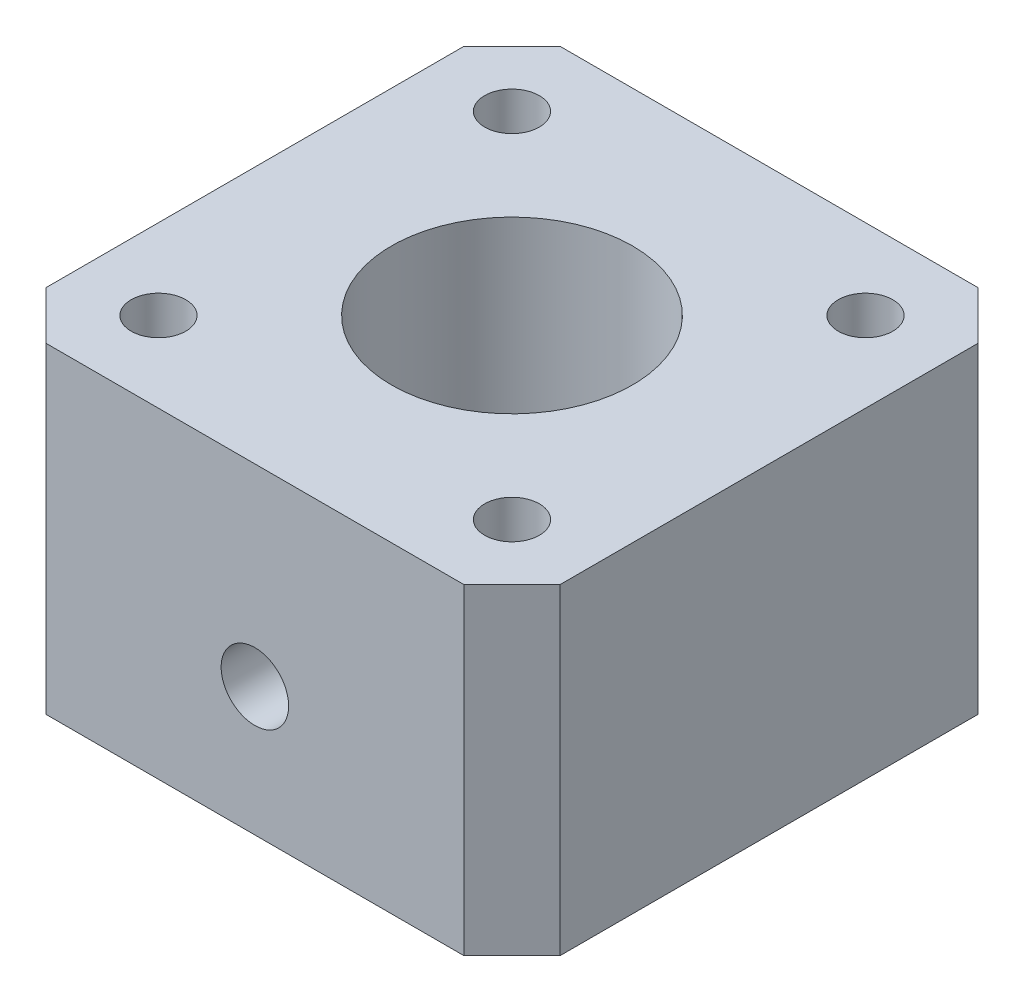
SolidWorks part; units mm, degrees
material "6061-T6 (SS)"
ref_plane "Front Plane" through (0, 0, 0) normal (0, 0, 1) x (1, 0, 0)
ref_plane "Top Plane" through (0, 0, 0) normal (0, 1, 0) x (1, 0, 0)
ref_plane "Right Plane" through (0, 0, 0) normal (1, 0, 0) x (0, 0, -1)
sketch "Sketch1" plane through (0, 0, 0) normal (0, 1, 0) x (1, 0, 0)
  line L0 (-16, 13) -> (-13, 16)
  line L1 (-13, 16) -> (13, 16)
  line L2 (-16, 13) -> (-16, -13)
  line L3 (-13, -16) -> (13, -16)
  line L4 (16, 13) -> (16, -13)
  line L5 (13, 16) -> (16, 13)
  line L6 (13, -16) -> (16, -13)
  line L7 (-16, -13) -> (-13, -16)
  line L8 (-16, 16) -> (-13, 16) construction
  line L9 (-16, 16) -> (-16, 13) construction
  circle A0 centre (0, 0) radius 7.5
  point P3 (-16, 16)
  point P4 (16, -16)
  point P5 (-16, -16)
  point P6 (16, 16)
  point P15 (-16, 0)
  point P16 (0, 16)
  point P17 (0, -16)
  point P18 (16, 0)
  dimension "D1" = 32
  dimension "D3" = 15
  dimension "D2" = 3
extrude "Boss-Extrude1" add sketch "Sketch1" along normal blind 20
sketch "Sketch2" plane through (0, 0, 16) normal (0, 0, 1) x (1, 0, 0)
  point P1 (0, 8)
  dimension "D1" = 8
hole_wizard "M5x0.8 Tapped Hole1" positions "Sketch2" profile "Sketch3" tap size "M5x0.8" standard "ANSI Metric"
cosmetic thread "Hole Thread1" parameters "D1"=10, "D2"=5
sketch "Sketch3" plane through (0, 8, 16) normal (1, 0, 0) x (0, -1, 0)
  line L0 (0, 0) -> (0, 17.2608)
  line L1 (0, 17.2608) -> (2.1, 15.999)
  line L2 (2.1, 15.999) -> (2.1, 0)
  line L5 (2.1, 0) -> (0, 0)
  line L10 (0, 17.2608) -> (-2.1, 15.999) construction
  line L11 (0, -6.35) -> (0, 107.95) construction
  dimension "Tap Drill Dia." = 4.2
  dimension "Tap Drill Depth" = 15.999
  dimension "Drill Angle" = 118
sketch "Sketch4" plane through (0, 0, 0) normal (0, -1, 0) x (-1, 0, 0)
  line L0 (-11, 11) -> (-11, -11) construction
  line L1 (-11, -11) -> (11, -11) construction
  line L2 (11, -11) -> (11, 11) construction
  line L3 (11, 11) -> (-11, 11) construction
  line L5 (-11, -11) -> (11, 11) construction
  line L7 (-11, 11) -> (11, -11) construction
  point P0 (-11, 11)
  point P2 (11, 11)
  point P4 (11, -11)
  point P6 (-11, -11)
  dimension "D1" = 22
hole_wizard "CBORE for M3 SHCS1" positions "Sketch4" profile "Sketch5" counterbore size "M3" standard "ANSI Metric" end condition through all
sketch "Sketch5" plane through (11, 0, -11) normal (1, 0, 0) x (0, 0, -1)
  line L0 (0, 0) -> (0, 20)
  line L1 (0, 20) -> (1.7, 20)
  line L3 (1.7, 20) -> (1.7, 3)
  line L4 (1.7, 3) -> (3.25, 3)
  line L5 (3.25, 3) -> (3.25, 0)
  line L7 (3.25, 0) -> (0, 0)
  line L11 (0, -6.35) -> (0, 107.95) construction
  dimension "Thru Hole Dia." = 3.4
  dimension "Thru Hole Depth" = 20
  dimension "C'Bore Dia." = 6.5
  dimension "C'Bore Depth" = 3
